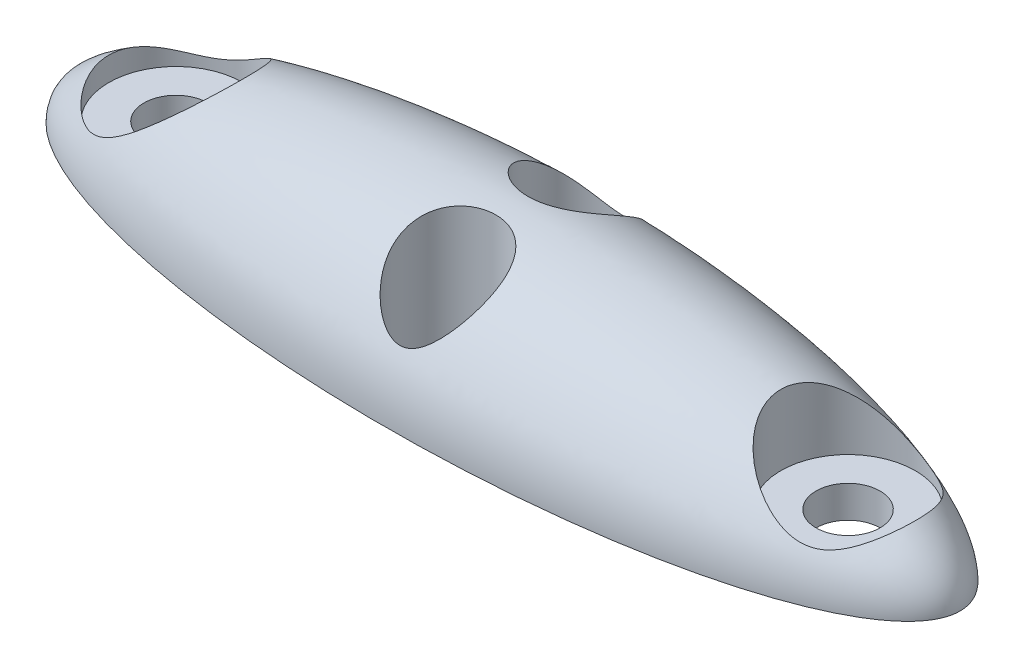
SolidWorks part; units mm, degrees
ref_plane "Front Plane" through (0, 0, 0) normal (0, 0, 1) x (1, 0, 0)
ref_plane "Top Plane" through (0, 0, 0) normal (0, 1, 0) x (1, 0, 0)
ref_plane "Right Plane" through (0, 0, 0) normal (1, 0, 0) x (0, 0, -1)
sketch "Sketch1" plane through (0, 0, 0) normal (0, 0, 1) x (1, 0, 0)
  line L0 (-14, 0) -> (14, 0) construction
  line L1 (-14, 0) -> (14, 0)
  circle A0 centre (-10.75, 0) radius 1 construction
  circle A1 centre (10.75, 0) radius 1 construction
  ellipse E0 centre (0, 0) end of major axis (14, 0) minor radius 4 (14, 0) -> (-14, 0) ccw
  dimension "D3" = 2
  dimension "D1" = 14
  dimension "D2" = 4
  dimension "D4" = 3.25
  dimension "D5" = 3.25
revolve "Revolve1" add sketch "Sketch1" angle 360 about L0
sketch "Sketch2" plane through (0, 0, 0) normal (0, 0, 1) x (1, 0, 0)
  line L1 (-26.9158, 0) -> (23.719, 0)
  line L2 (-26.9158, 0) -> (-26.9158, -13.0728)
  line L3 (-26.9158, -13.0728) -> (23.719, -13.0728)
  line L4 (23.719, 0) -> (23.719, -13.0728)
extrude "Cut-Extrude1" cut sketch "Sketch2" against normal through all both and the other way through all
sketch "Sketch3" plane through (0, 0, 0) normal (0, -1, 0) x (1, 0, 0)
  line L0 (-14, 0) -> (14, 0) construction
  circle A0 centre (-10.5, 0) radius 1
  circle A1 centre (10.5, 0) radius 1
  ellipse E0 centre (0, 0) end of major axis (14, 0) minor radius 4 (-14, 0) -> (14, 0) ccw construction
  ellipse E1 centre (0, 0) end of major axis (14, 0) minor radius 4 (14, 0) -> (-14, 0) ccw construction
  dimension "D1" = 2
  dimension "D2" = 3.5
  dimension "D3" = 3.5
extrude "Cut-Extrude2" cut sketch "Sketch3" against normal through all
ref_plane "Plane1" through (0, 1, 0) normal (0, -1, 0) x (-1, 0, 0)
sketch "Sketch4" plane through (0, 1, 0) normal (0, -1, 0) x (-1, 0, 0)
  circle A0 centre (10.5, 0) radius 2.1
  circle A1 centre (-10.5, 0) radius 2.1
  dimension "D1" = 4.2
extrude "Cut-Extrude3" cut sketch "Sketch4" against normal through all
sketch "Sketch5" plane through (0, 0, 0) normal (0, -1, 0) x (1, 0, 0)
  line L0 (-10.5, 0) -> (10.5, 0) construction
  line L1 (0, 2) -> (0, -2) construction
  circle A0 centre (0, 2) radius 1.5
  circle A1 centre (0, -2) radius 1.5
  point P8 (0, 0)
  dimension "D1" = 3
  dimension "D2" = 4
  dimension "D3" = 0
extrude "Cut-Extrude4" cut sketch "Sketch5" against normal through all
